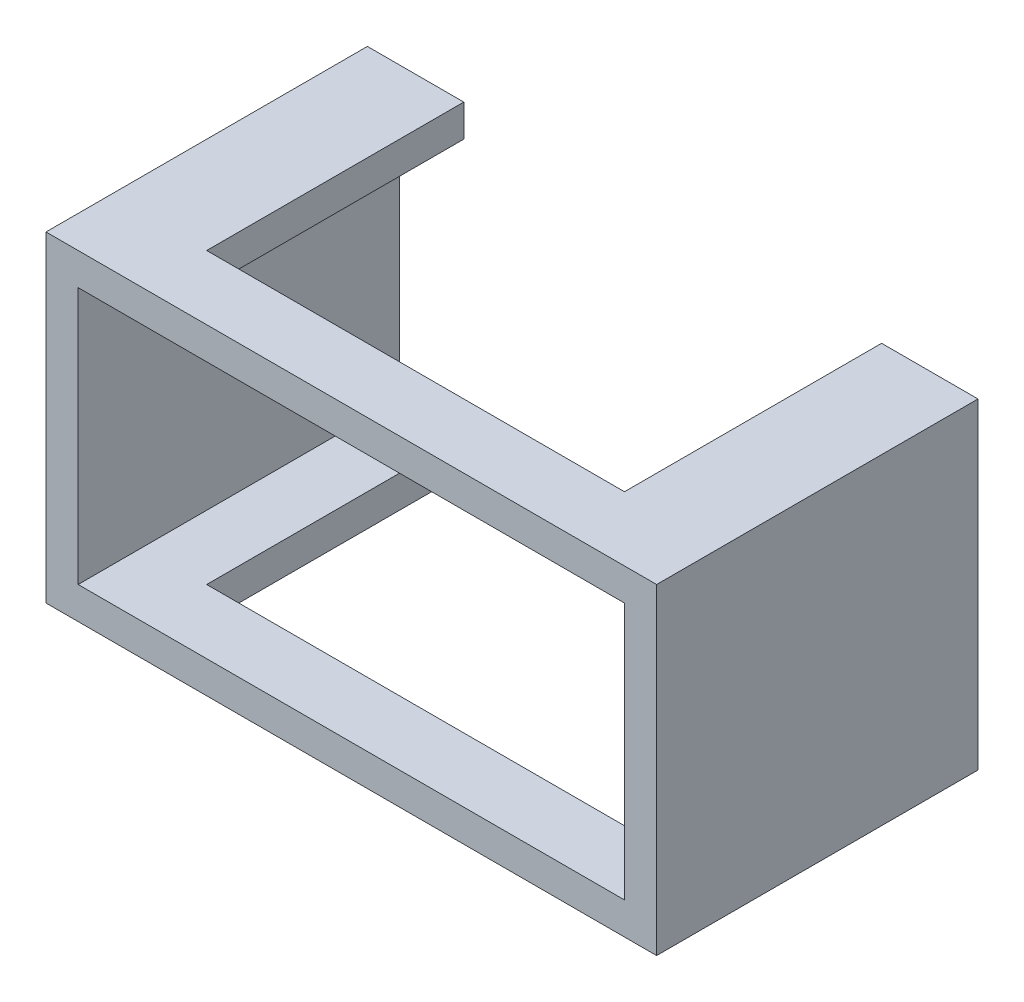
SolidWorks part; units mm, degrees
ref_plane "Front Plane" through (0, 0, 0) normal (0, 0, 1) x (1, 0, 0)
ref_plane "Top Plane" through (0, 0, 0) normal (0, 1, 0) x (1, 0, 0)
ref_plane "Right Plane" through (0, 0, 0) normal (1, 0, 0) x (0, 0, -1)
sketch "Sketch1" plane through (0, 0, 0) normal (0, 0, 1) x (1, 0, 0)
  line L1 (-9.6301, 7.2226) -> (9.3699, 7.2226)
  line L2 (-9.6301, 7.2226) -> (-9.6301, -2.7774)
  line L3 (-9.6301, -2.7774) -> (9.3699, -2.7774)
  line L4 (9.3699, 7.2226) -> (9.3699, -2.7774)
  dimension "D1" = 19
  dimension "D2" = 10
extrude "Boss-Extrude1" add sketch "Sketch1" along normal blind 10
sketch "Sketch2" plane through (0, 0, 10) normal (0, 0, 1) x (1, 0, 0)
  line L0 (-0.1301, 7.2226) -> (-0.1301, -2.7774) construction
  line L1 (-8.6301, 6.2226) -> (8.3699, 6.2226)
  line L2 (-8.6301, 6.2226) -> (-8.6301, -1.7774)
  line L3 (-8.6301, -1.7774) -> (8.3699, -1.7774)
  line L4 (8.3699, 6.2226) -> (8.3699, -1.7774)
  line L7 (9.3699, 7.2226) -> (-9.6301, 7.2226) construction
  line L8 (-9.6301, -2.7774) -> (9.3699, -2.7774) construction
  line L9 (-9.6301, 2.2226) -> (9.3699, 2.2226) construction
  line L10 (-9.6301, 7.2226) -> (-9.6301, -2.7774) construction
  line L11 (9.3699, -2.7774) -> (9.3699, 7.2226) construction
  dimension "D1" = 17
  dimension "D2" = 8
  dimension "D3" = 4
  dimension "D4" = 8.5
extrude "Cut-Extrude1" cut sketch "Sketch2" against normal blind 12
sketch "Sketch3" plane through (0, 0, 0) normal (0, 0, 1) x (1, 0, 0)
  line L0 (-8.6301, 6.2226) -> (-8.6301, -1.7774) construction
  line L1 (-6.6301, 7.6051) -> (6.3699, 7.6051)
  line L2 (-6.6301, 7.6051) -> (-6.6301, -2.9148)
  line L3 (-6.6301, -2.9148) -> (6.3699, -2.9148)
  line L4 (6.3699, 7.6051) -> (6.3699, -2.9148)
  line L5 (8.3699, -1.7774) -> (8.3699, 6.2226) construction
  point P4 (-7.729, 7.6051)
  dimension "D1" = 2
  dimension "D2" = 2
extrude "Cut-Extrude3" cut sketch "Sketch3" along normal blind 8 contours L1 L4 L3 L2
